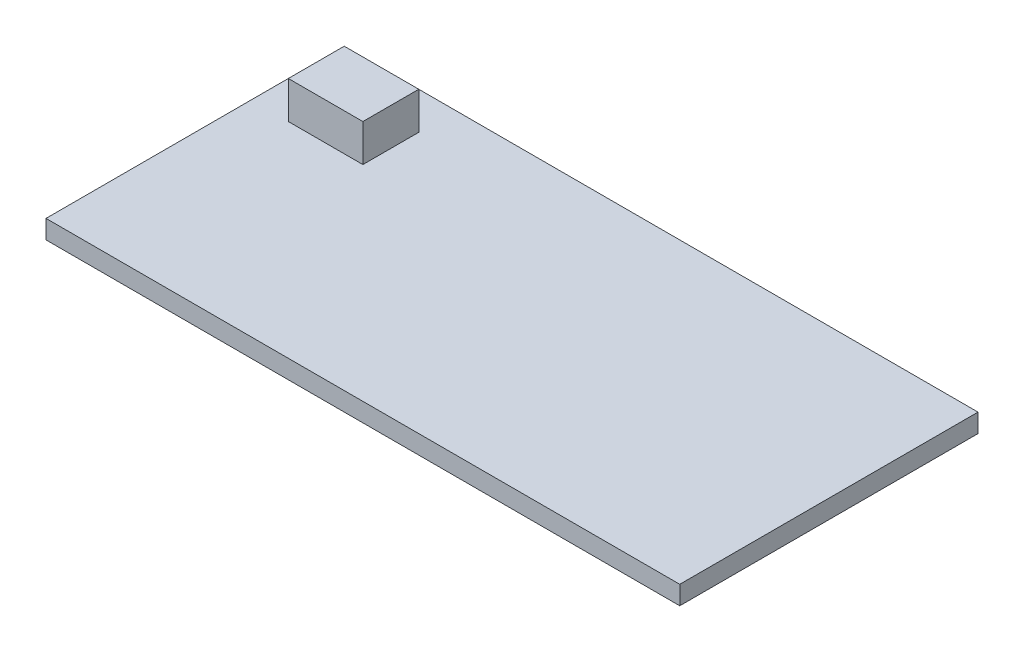
SolidWorks part; units mm, degrees
ref_plane "Front Plane" through (0, 0, 0) normal (0, 0, 1) x (1, 0, 0)
ref_plane "Top Plane" through (0, 0, 0) normal (0, 1, 0) x (1, 0, 0)
ref_plane "Right Plane" through (0, 0, 0) normal (1, 0, 0) x (0, 0, -1)
sketch "Sketch1" plane through (0, 0, 0) normal (0, 1, 0) x (1, 0, 0)
  line L1 (0, 0) -> (170, 0)
  line L2 (0, 0) -> (0, 80)
  line L3 (0, 80) -> (170, 80)
  line L4 (170, 0) -> (170, 80)
  dimension "D1" = 170
  dimension "D2" = 80
extrude "Boss-Extrude1" add sketch "Sketch1" along normal blind 5
sketch "Sketch2" plane through (0, 5, 0) normal (0, 1, 0) x (1, 0, 0)
  line L0 (0, 80) -> (0, 0) construction
  line L1 (10, 70) -> (30, 70)
  line L2 (10, 70) -> (10, 55)
  line L3 (10, 55) -> (30, 55)
  line L4 (30, 70) -> (30, 55)
  line L5 (170, 80) -> (0, 80) construction
  dimension "D1" = 20
  dimension "D2" = 15
  dimension "D3" = 10
  dimension "D4" = 10
extrude "Boss-Extrude2" add sketch "Sketch2" along normal blind 10
